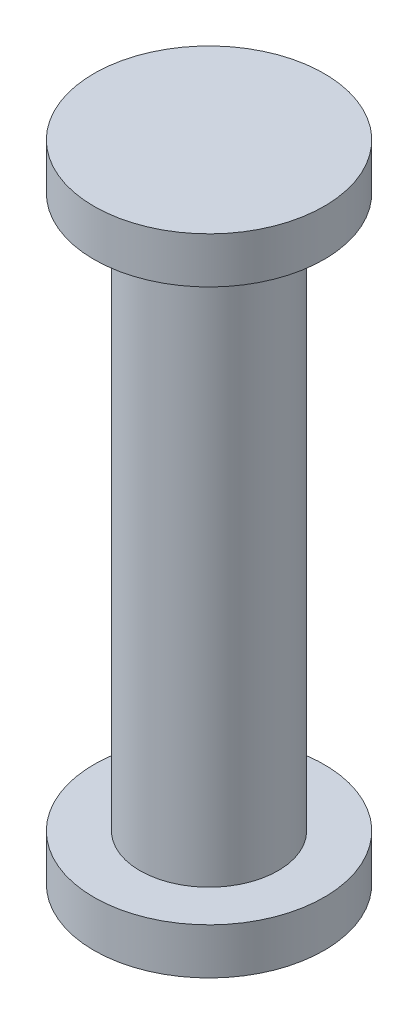
SolidWorks part; units mm, degrees
ref_plane "Front Plane" through (0, 0, 0) normal (0, 0, 1) x (1, 0, 0)
ref_plane "Top Plane" through (0, 0, 0) normal (0, 1, 0) x (1, 0, 0)
ref_plane "Right Plane" through (0, 0, 0) normal (1, 0, 0) x (0, 0, -1)
sketch "Sketch1" plane through (0, 0, 0) normal (0, 1, 0) x (1, 0, 0)
  circle A0 centre (0, 0) radius 2.5
extrude "Boss-Extrude1" add sketch "Sketch1" along normal blind 1
sketch "Sketch2" plane through (0, 1, 0) normal (0, 1, 0) x (1, 0, 0)
  circle A0 centre (0, 0) radius 1.5
extrude "Boss-Extrude2" add sketch "Sketch2" along normal blind 12
sketch "Sketch3" plane through (0, 13, 0) normal (0, 1, 0) x (1, 0, 0)
  circle A0 centre (0, 0) radius 2.5
extrude "Boss-Extrude3" add sketch "Sketch3" along normal blind 1
